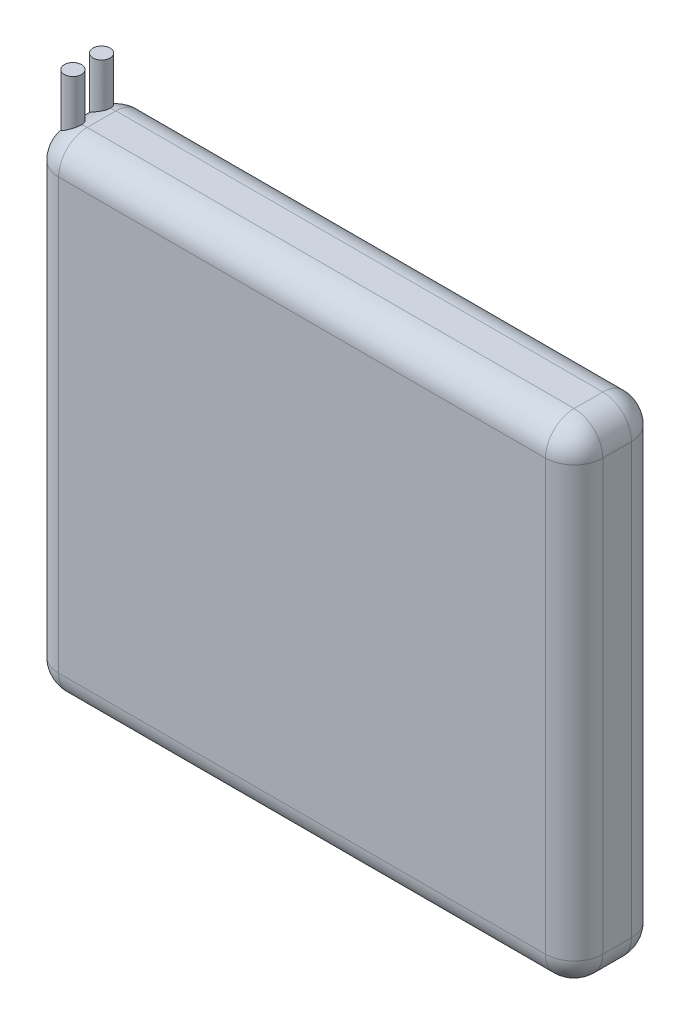
SolidWorks part; units mm, degrees
ref_plane "Plan de face" through (0, 0, 0) normal (0, 0, 1) x (1, 0, 0)
ref_plane "Plan de dessus" through (0, 0, 0) normal (0, 1, 0) x (1, 0, 0)
ref_plane "Plan de droite" through (0, 0, 0) normal (1, 0, 0) x (0, 0, -1)
sketch "Esquisse1" plane through (0, 0, 0) normal (0, 0, 1) x (1, 0, 0)
  line L1 (0, 0) -> (38, 0)
  line L2 (0, 0) -> (0, 34)
  line L3 (0, 34) -> (38, 34)
  line L4 (38, 0) -> (38, 34)
  dimension "D1" = 38
  dimension "D2" = 34
extrude "Boss.-Extru.1" add sketch "Esquisse1" along normal blind 6
fillet "Congé2" radius 2 12 edges at (19, 34, 6) (0, 34, 3) (19, 34, 0) (38, 17, 6) (38, 34, 3) (38, 17, 0) (0, 0, 3) (19, 0, 6) (38, 0, 3) (19, 0, 0) (0, 17, 6) (0, 17, 0)
sketch "Esquisse2" plane through (0, 34, 0) normal (0, 1, 0) x (1, 0, 0)
  circle A0 centre (1, -2) radius 0.6
  circle A1 centre (1, -4) radius 0.6
  point P2 (0, 0)
  point P8 (0, 0)
extrude "Boss.-Extru.2" add sketch "Esquisse2" along normal blind 3 and the other way blind 6
